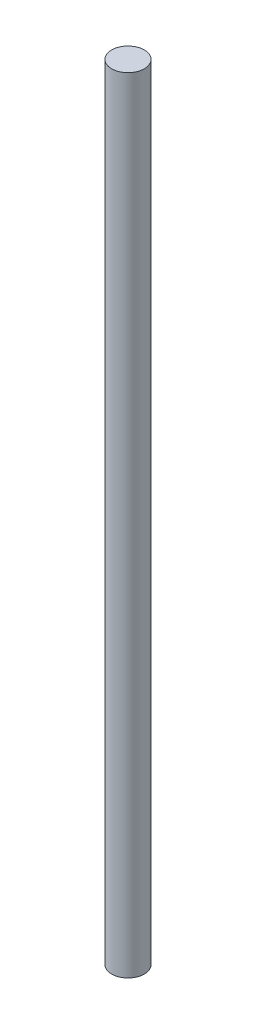
SolidWorks part; units mm, degrees
material "Plain Carbon Steel"
ref_plane "Front Plane" through (0, 0, 0) normal (0, 0, 1) x (1, 0, 0)
ref_plane "Top Plane" through (0, 0, 0) normal (0, 1, 0) x (1, 0, 0)
ref_plane "Right Plane" through (0, 0, 0) normal (1, 0, 0) x (0, 0, -1)
sketch "Sketch1" plane through (0, 0, 0) normal (0, 1, 0) x (1, 0, 0)
  circle A0 centre (0, 0) radius 6.35
  dimension "D1" = 12.7
extrude "Boss-Extrude1" add sketch "Sketch1" along normal blind 304.8
sketch "Sketch4" plane through (0, 0, 0) normal (0, -1, 0) x (1, 0, 0)
  line L0 (-0.763, 4.6367) -> (-0.0949, 4.6367)
  line L7 (0, 1.4617) -> (-0.8585, 1.4617)
  point P4 (-0.4289, 4.6367)
  dimension "D1" = 0.8585
  dimension "D2" = 3.175
sketch "Sketch6" plane through (0, 0, 0) normal (0, -1, 0) x (1, 0, 0)
  circle A0 centre (0, 0) radius 6.35 construction
  circle A1 centre (0, 0) radius 6.35
curve "Helix/Spiral1" pitch 2.1082 height 304.8 turns 144.5783
sketch "Sketch7" plane through (0, 304.8, 0) normal (0, 1, 0) x (1, 0, 0)
  point P0 (3, -5.5967)
ref_plane "Plane1" through (3, 304.8, 5.5967) normal (0.4724, 0, 0.8814) x (0.8814, 0, -0.4724)
sketch "Sketch8" plane through (0, 0, 0) normal (1, 0, 0) x (0, 0, -1)
  line L0 (6.35, 305.327) -> (6.35, 304.273)
  line L1 (6.35, 304.273) -> (7.4041, 304.5456)
  line L2 (7.4041, 304.5456) -> (7.4041, 305.0544)
  line L3 (7.4041, 305.0544) -> (6.35, 305.327)
  line L4 (6.35, 304.273) -> (6.35, 300.6583) construction
  line L5 (6.35, 304.273) -> (10.0789, 304.273) construction
  point P3 (7.4041, 304.8)
  point P5 (6.35, 304.8)
  dimension "D1" = 1.0541
  dimension "D2" = 1.0541
  dimension "D4" = 14.5
sketch "Sketch9" plane through (0, 304.8, 0) normal (0, 1, 0) x (1, 0, 0)
  line L1 (-13.3747, -9.2902) -> (15.3962, -9.2902)
  line L2 (-13.3747, -9.2902) -> (-13.3747, 11.3018)
  line L3 (-13.3747, 11.3018) -> (15.3962, 11.3018)
  line L4 (15.3962, -9.2902) -> (15.3962, 11.3018)
sketch "Sketch10" plane through (0, 0, 0) normal (0, -1, 0) x (1, 0, 0)
  line L1 (21.5646, -16.2755) -> (-22.383, -16.2755)
  line L2 (21.5646, -16.2755) -> (21.5646, 16.8796)
  line L3 (21.5646, 16.8796) -> (-22.383, 16.8796)
  line L4 (-22.383, -16.2755) -> (-22.383, 16.8796)
